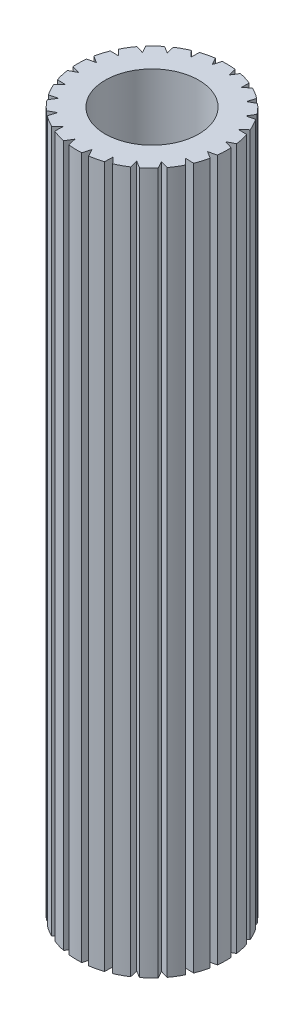
SolidWorks part; units mm, degrees
ref_plane "前视基准面" through (0, 0, 0) normal (0, 0, 1) x (1, 0, 0)
ref_plane "上视基准面" through (0, 0, 0) normal (0, 1, 0) x (1, 0, 0)
ref_plane "右视基准面" through (0, 0, 0) normal (1, 0, 0) x (0, 0, -1)
sketch "草图1" plane through (0, 0, 0) normal (0, 1, 0) x (1, 0, 0)
  line L0 (-0.2281, 1.5837) -> (-0.144, 1.4291)
  line L1 (-0.144, 1.4291) -> (-0.0944, 1.5972)
  line L2 (0.2308, 1.4177) -> (0.3222, 1.5672)
  line L3 (0.1895, 1.5887) -> (0.2308, 1.4177)
  line L4 (0.5898, 1.3097) -> (0.7168, 1.4304)
  line L5 (0.5943, 1.4855) -> (0.5898, 1.3097)
  line L6 (0.9087, 1.1124) -> (1.0626, 1.1962)
  line L7 (0.9585, 1.2811) -> (0.9087, 1.1124)
  line L8 (1.1657, 0.8393) -> (1.336, 0.8804)
  line L9 (1.2574, 0.9894) -> (1.1657, 0.8393)
  line L10 (1.3432, 0.509) -> (1.5183, 0.5046)
  line L11 (1.4707, 0.6302) -> (1.3432, 0.509)
  line L12 (1.4291, 0.144) -> (1.5972, 0.0944)
  line L13 (1.5837, 0.2281) -> (1.4291, 0.144)
  line L14 (1.4177, -0.2308) -> (1.5672, -0.3222)
  line L15 (1.5887, -0.1895) -> (1.4177, -0.2308)
  line L16 (1.3097, -0.5898) -> (1.4304, -0.7168)
  line L17 (1.4855, -0.5943) -> (1.3097, -0.5898)
  line L18 (1.1124, -0.9087) -> (1.1962, -1.0626)
  line L19 (1.2811, -0.9585) -> (1.1124, -0.9087)
  line L20 (0.8393, -1.1657) -> (0.8804, -1.336)
  line L21 (0.9894, -1.2574) -> (0.8393, -1.1657)
  line L22 (0.509, -1.3432) -> (0.5046, -1.5183)
  line L23 (0.6302, -1.4707) -> (0.509, -1.3432)
  line L24 (0.144, -1.4291) -> (0.0944, -1.5972)
  line L25 (0.2281, -1.5837) -> (0.144, -1.4291)
  line L26 (-0.2308, -1.4177) -> (-0.3222, -1.5672)
  line L27 (-0.1895, -1.5887) -> (-0.2308, -1.4177)
  line L28 (-0.5898, -1.3097) -> (-0.7168, -1.4304)
  line L29 (-0.5943, -1.4855) -> (-0.5898, -1.3097)
  line L30 (-0.9087, -1.1124) -> (-1.0626, -1.1962)
  line L31 (-0.9585, -1.2811) -> (-0.9087, -1.1124)
  line L32 (-1.1657, -0.8393) -> (-1.336, -0.8804)
  line L33 (-1.2574, -0.9894) -> (-1.1657, -0.8393)
  line L34 (-1.3432, -0.509) -> (-1.5183, -0.5046)
  line L35 (-1.4707, -0.6302) -> (-1.3432, -0.509)
  line L36 (-1.4291, -0.144) -> (-1.5972, -0.0944)
  line L37 (-1.5837, -0.2281) -> (-1.4291, -0.144)
  line L38 (-1.4177, 0.2308) -> (-1.5672, 0.3222)
  line L39 (-1.5887, 0.1895) -> (-1.4177, 0.2308)
  line L40 (-1.3097, 0.5898) -> (-1.4304, 0.7168)
  line L41 (-1.4855, 0.5943) -> (-1.3097, 0.5898)
  line L42 (-1.1124, 0.9087) -> (-1.1962, 1.0626)
  line L43 (-1.2811, 0.9585) -> (-1.1124, 0.9087)
  line L44 (-0.8393, 1.1657) -> (-0.8804, 1.336)
  line L45 (-0.9894, 1.2574) -> (-0.8393, 1.1657)
  line L46 (-0.509, 1.3432) -> (-0.5046, 1.5183)
  line L47 (-0.6302, 1.4707) -> (-0.509, 1.3432)
  arc A0 (-1.2811, 0.9585) -> (-1.4304, 0.7168) centre (0, 0) ccw
  circle A1 centre (0, 0) radius 1
  arc A2 (-0.9894, 1.2574) -> (-1.1962, 1.0626) centre (0, 0) ccw
  arc A3 (-0.6302, 1.4707) -> (-0.8804, 1.336) centre (0, 0) ccw
  arc A4 (-0.2281, 1.5837) -> (-0.5046, 1.5183) centre (0, 0) ccw
  arc A5 (0.1895, 1.5887) -> (-0.0944, 1.5972) centre (0, 0) ccw
  arc A6 (0.5943, 1.4855) -> (0.3222, 1.5672) centre (0, 0) ccw
  arc A7 (0.9585, 1.2811) -> (0.7168, 1.4304) centre (0, 0) ccw
  arc A8 (1.2574, 0.9894) -> (1.0626, 1.1962) centre (0, 0) ccw
  arc A9 (1.4707, 0.6302) -> (1.336, 0.8804) centre (0, 0) ccw
  arc A10 (1.5837, 0.2281) -> (1.5183, 0.5046) centre (0, 0) ccw
  arc A11 (1.5887, -0.1895) -> (1.5972, 0.0944) centre (0, 0) ccw
  arc A12 (1.4855, -0.5943) -> (1.5672, -0.3222) centre (0, 0) ccw
  arc A13 (1.2811, -0.9585) -> (1.4304, -0.7168) centre (0, 0) ccw
  arc A14 (0.9894, -1.2574) -> (1.1962, -1.0626) centre (0, 0) ccw
  arc A15 (0.6302, -1.4707) -> (0.8804, -1.336) centre (0, 0) ccw
  arc A16 (0.2281, -1.5837) -> (0.5046, -1.5183) centre (0, 0) ccw
  arc A17 (-0.1895, -1.5887) -> (0.0944, -1.5972) centre (0, 0) ccw
  arc A18 (-0.5943, -1.4855) -> (-0.3222, -1.5672) centre (0, 0) ccw
  arc A19 (-0.9585, -1.2811) -> (-0.7168, -1.4304) centre (0, 0) ccw
  arc A20 (-1.2574, -0.9894) -> (-1.0626, -1.1962) centre (0, 0) ccw
  arc A21 (-1.4707, -0.6302) -> (-1.336, -0.8804) centre (0, 0) ccw
  arc A22 (-1.5837, -0.2281) -> (-1.5183, -0.5046) centre (0, 0) ccw
  arc A23 (-1.5887, 0.1895) -> (-1.5972, -0.0944) centre (0, 0) ccw
  arc A24 (-1.4855, 0.5943) -> (-1.5672, 0.3222) centre (0, 0) ccw
  point P79 (0, 0)
  dimension "D1" = 3.2
  dimension "D2" = 2
  dimension "D3" = 45
  dimension "D4" = 24
extrude "凸台-拉伸1" add sketch "草图1" along normal blind 15
